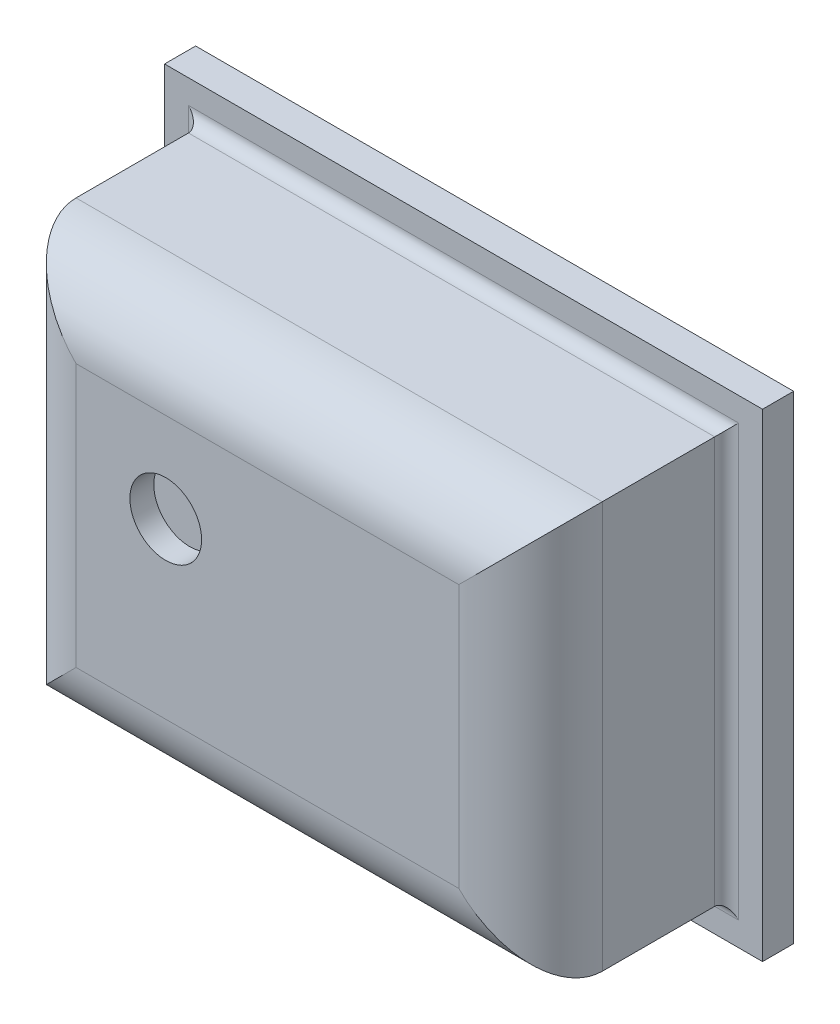
SolidWorks part; units mm, degrees
ref_plane "Plan de face" through (0, 0, 0) normal (0, 0, 1) x (1, 0, 0)
ref_plane "Plan de dessus" through (0, 0, 0) normal (0, 1, 0) x (1, 0, 0)
ref_plane "Plan de droite" through (0, 0, 0) normal (1, 0, 0) x (0, 0, -1)
sketch "Esquisse1" plane through (0, 0, 0) normal (0, 0, 1) x (1, 0, 0)
  line L1 (-1.25, 1) -> (1.25, 1)
  line L2 (-1.25, 1) -> (-1.25, -1)
  line L3 (-1.25, -1) -> (1.25, -1)
  line L4 (1.25, 1) -> (1.25, -1)
  line L5 (-1.25, 1) -> (1.25, -1) construction
  line L6 (-1.25, -1) -> (1.25, 1) construction
  point P0 (0, 0)
  dimension "D1" = 2
  dimension "D2" = 2.5
extrude "Boss.-Extru.1" add sketch "Esquisse1" along normal blind 0.13
sketch "Esquisse2" plane through (0, 0, 0.13) normal (0, 0, 1) x (1, 0, 0)
  line L1 (-1.1, 0.85) -> (1.1, 0.85)
  line L2 (-1.1, 0.85) -> (-1.1, -0.85)
  line L3 (-1.1, -0.85) -> (1.1, -0.85)
  line L4 (1.1, 0.85) -> (1.1, -0.85)
  line L5 (-1.1, 0.85) -> (1.1, -0.85) construction
  line L6 (-1.1, -0.85) -> (1.1, 0.85) construction
  point P0 (0, 0)
  dimension "D1" = 1.7
  dimension "D2" = 2.2
extrude "Boss.-Extru.2" add sketch "Esquisse2" along normal blind 0.82
fillet "Congé1" radius 0.3 4 edges at (0, -0.85, 0.95) (-1.1, 0, 0.95) (0, 0.85, 0.95) (1.1, 0, 0.95)
sketch "Esquisse3" plane through (0, 0, 0.95) normal (0, 0, 1) x (1, 0, 0)
  line L0 (-1.25, 1) -> (-1.25, -1) construction
  line L1 (1.25, 1) -> (-1.25, 1) construction
  circle A0 centre (-0.425, 0.175) radius 0.15
  dimension "D3" = 0.3
  dimension "D1" = 0.825
  dimension "D2" = 0.825
extrude "Enlèv. mat.-Extru.1" cut sketch "Esquisse3" against normal blind 0.1
fillet "Congé2" radius 0.05 4 edges at (0, 0.85, 0.13) (1.1, 0, 0.13) (-1.1, 0, 0.13) (0, -0.85, 0.13)
